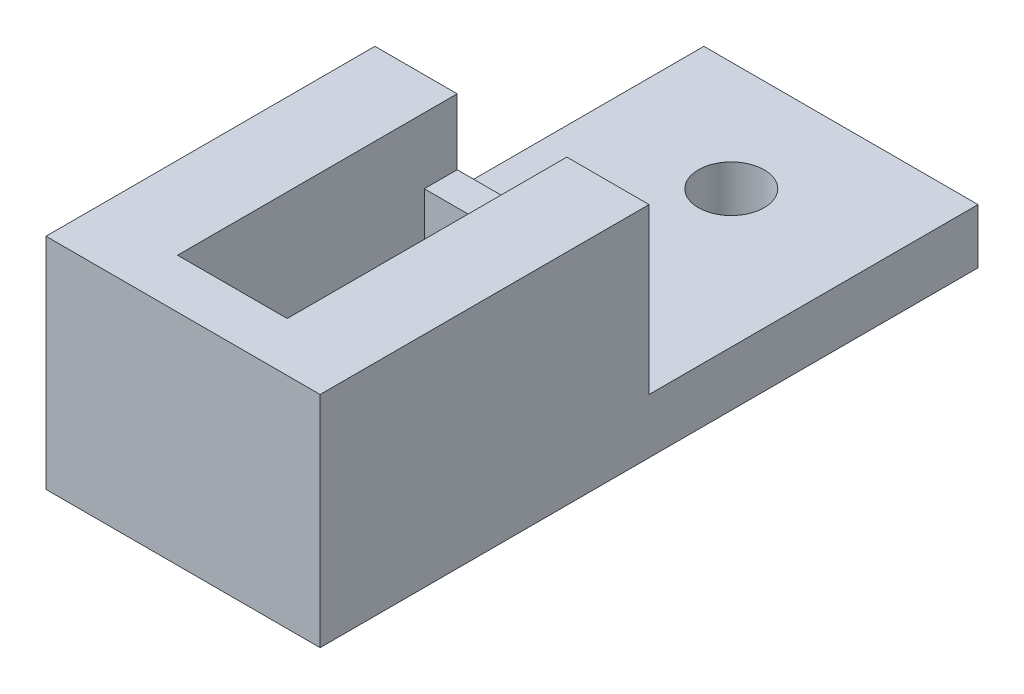
SolidWorks part; units mm, degrees
ref_plane "Front Plane" through (0, 0, 0) normal (0, 0, 1) x (1, 0, 0)
ref_plane "Top Plane" through (0, 0, 0) normal (0, 1, 0) x (1, 0, 0)
ref_plane "Right Plane" through (0, 0, 0) normal (1, 0, 0) x (0, 0, -1)
sketch "Sketch1" plane through (0, 0, 0) normal (0, 1, 0) x (1, 0, 0)
  line L1 (-15.875, 38.1) -> (15.875, 38.1)
  line L2 (-15.875, 38.1) -> (-15.875, -38.1)
  line L3 (-15.875, -38.1) -> (15.875, -38.1)
  line L4 (15.875, 38.1) -> (15.875, -38.1)
  line L5 (-15.875, 38.1) -> (15.875, -38.1) construction
  line L6 (-15.875, -38.1) -> (15.875, 38.1) construction
  point P0 (0, 0)
  dimension "D1" = 31.75
  dimension "D2" = 76.2
extrude "Boss-Extrude1" add sketch "Sketch1" along normal blind 6.35
sketch "Sketch2" plane through (0, 6.35, 0) normal (0, 1, 0) x (1, 0, 0)
  line L0 (0, 0) -> (0, 25.4) construction
  line L1 (0, 25.4) -> (0, 38.1) construction
  line L2 (15.875, 38.1) -> (-15.875, 38.1) construction
  circle A0 centre (0, 25.4) radius 3.81
  dimension "D1" = 7.62
  dimension "D2" = 12.7
extrude "Cut-Extrude1" cut sketch "Sketch2" against normal through all
sketch "Sketch3" plane through (0, 6.35, 0) normal (0, 1, 0) x (1, 0, 0)
  line L0 (15.875, -38.1) -> (15.875, 38.1) construction
  line L1 (-15.875, -38.1) -> (15.875, -38.1)
  line L2 (-15.875, -38.1) -> (-15.875, 0)
  line L3 (-15.875, 0) -> (15.875, 0)
  line L4 (15.875, -38.1) -> (15.875, 0)
  line L5 (15.875, 38.1) -> (-15.875, 38.1) construction
  dimension "D1" = 38.1
extrude "Boss-Extrude2" add sketch "Sketch3" along normal blind 19.05
sketch "Sketch4" plane through (0, 25.4, 0) normal (0, 1, 0) x (1, 0, 0)
  line L0 (0, 0) -> (0, -19.05) construction
  line L1 (-6.35, 0) -> (6.35, 0)
  line L2 (-6.35, 0) -> (-6.35, -38.1)
  line L3 (-6.35, -38.1) -> (6.35, -38.1)
  line L4 (6.35, 0) -> (6.35, -38.1)
  line L5 (-6.35, 0) -> (6.35, -38.1) construction
  line L6 (-6.35, -38.1) -> (6.35, 0) construction
  line L7 (15.875, 0) -> (-15.875, 0) construction
  point P0 (0, -19.05)
  dimension "D1" = 12.7
  dimension "D2" = 38.1
extrude "Cut-Extrude2" cut sketch "Sketch4" against normal up to surface (19.05 mm away) up to face at (0, 6.35, -19.05)
sketch "Sketch5" plane through (0, 6.35, 0) normal (0, 1, 0) x (1, 0, 0)
  line L0 (-6.35, -38.1) -> (-6.35, 0) construction
  line L1 (-6.35, -3.81) -> (6.35, -3.81)
  line L2 (-6.35, -3.81) -> (-6.35, -32.385)
  line L3 (-6.35, -32.385) -> (6.35, -32.385)
  line L4 (6.35, -3.81) -> (6.35, -32.385)
  line L5 (6.35, -38.1) -> (6.35, 0) construction
  line L6 (-6.35, 0) -> (-15.875, 0) construction
  dimension "D1" = 3.81
  dimension "D2" = 28.575
extrude "Cut-Extrude3" cut sketch "Sketch5" against normal through all
sketch "Sketch6" plane through (0, 6.35, 0) normal (0, 1, 0) x (1, 0, 0)
  line L1 (6.35, -3.81) -> (-6.35, -3.81)
  line L2 (6.35, -3.81) -> (6.35, 0)
  line L3 (6.35, 0) -> (-6.35, 0)
  line L4 (-6.35, -3.81) -> (-6.35, 0)
extrude "Boss-Extrude3" add sketch "Sketch6" along normal blind 11.43
sketch "Sketch7" plane through (-6.35, 0, 0) normal (1, 0, 0) x (0, 0, -1)
  line L0 (-32.385, 17.78) -> (-27.305, 17.78)
  line L1 (-33.655, 17.78) -> (-32.385, 17.78) construction
  line L2 (-33.655, 17.78) -> (-33.655, 11.43) construction
  line L3 (-33.655, 11.43) -> (-32.385, 11.43) construction
  line L4 (-27.305, 17.78) -> (-27.305, 11.43)
  line L5 (-33.655, 17.78) -> (-27.305, 11.43) construction
  line L6 (-33.655, 11.43) -> (-27.305, 17.78) construction
  line L7 (-38.1, 6.35) -> (-32.385, 6.35) construction
  line L8 (-32.385, 0) -> (-32.385, 6.35) construction
  line L9 (-32.385, 6.35) -> (-32.385, 11.43)
  line L10 (-32.385, 17.78) -> (-32.385, 25.4)
  line L11 (0, 25.4) -> (-38.1, 25.4) construction
  line L12 (-32.385, 25.4) -> (-38.1, 25.4)
  line L13 (-38.1, 25.4) -> (-38.1, 6.35)
  line L14 (-38.1, 6.35) -> (-32.385, 6.35)
  line L15 (-32.385, 11.43) -> (-27.305, 11.43)
  point P0 (-30.48, 14.605)
  point P16 (-34.1272, 11.43)
  dimension "D1" = 6.35
  dimension "D2" = 11.43
  dimension "D3" = 6.35
  dimension "D4" = 5.08
extrude "Boss-Extrude4" add sketch "Sketch7" along normal up to next
